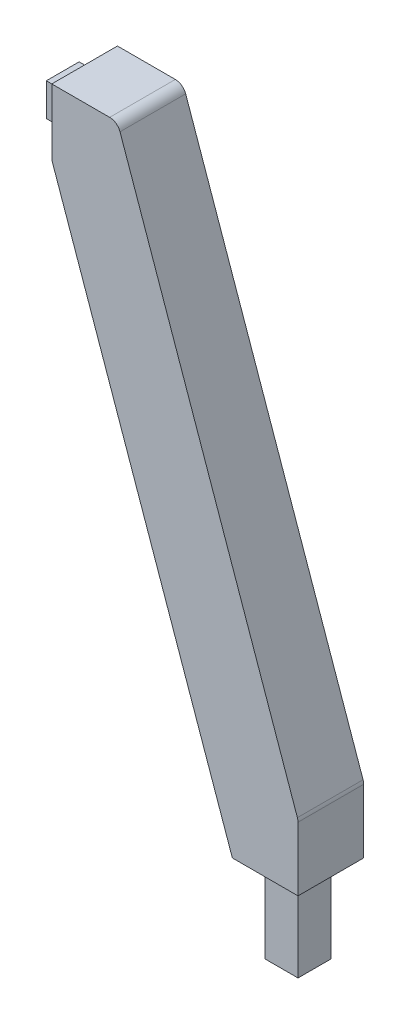
SolidWorks part; units mm, degrees
ref_plane "Front Plane" through (0, 0, 0) normal (0, 0, 1) x (1, 0, 0)
ref_plane "Top Plane" through (0, 0, 0) normal (0, 1, 0) x (1, 0, 0)
ref_plane "Right Plane" through (0, 0, 0) normal (1, 0, 0) x (0, 0, -1)
sketch "Sketch1" plane through (0, 0, 0) normal (0, 0, 1) x (1, 0, 0)
  line L0 (0, 0) -> (-30, 0)
  line L1 (-112.5, 235) -> (-112.5, 265)
  line L3 (-112.5, 235) -> (-30, 0)
  line L4 (-112.5, 265) -> (-82.5, 265)
  line L6 (0, 0) -> (0, 30)
  line L7 (0, 30) -> (-82.5, 265)
  dimension "D1" = 30
  dimension "D2" = 30
extrude "Boss-Extrude1" add sketch "Sketch1" along normal blind 30
sketch "Sketch2" plane through (-112.5, 0, 0) normal (-1, 0, 0) x (0, 0, 1)
  line L1 (7.51, 257.49) -> (22.49, 257.49)
  line L2 (7.51, 257.49) -> (7.51, 242.51)
  line L3 (7.51, 242.51) -> (22.49, 242.51)
  line L4 (22.49, 257.49) -> (22.49, 242.51)
  line L5 (30, 235) -> (0, 235) construction
  line L6 (30, 265) -> (30, 235) construction
  line L7 (0, 265) -> (0, 235) construction
  dimension "D2" = 7.51
  dimension "D3" = 7.51
  dimension "D4" = 7.51
extrude "Boss-Extrude2" add sketch "Sketch2" along normal blind 10
sketch "Sketch3" plane through (0, 0, 0) normal (0, -1, 0) x (1, 0, 0)
  line L1 (-30, 30) -> (-30, 0) construction
  line L2 (-22.49, 22.49) -> (-7.51, 22.49)
  line L3 (-22.49, 22.49) -> (-22.49, 7.51)
  line L4 (-22.49, 7.51) -> (-7.51, 7.51)
  line L5 (-7.51, 22.49) -> (-7.51, 7.51)
  line L6 (-30, 30) -> (0, 30) construction
  line L8 (-30, 0) -> (0, 0) construction
  dimension "D1" = 7.51
  dimension "D2" = 7.51
  dimension "D4" = 7.51
extrude "Boss-Extrude3" add sketch "Sketch3" along normal blind 40
fillet "Fillet1" radius 5 2 edges at (0, 30, 15) (-82.5, 265, 15)
